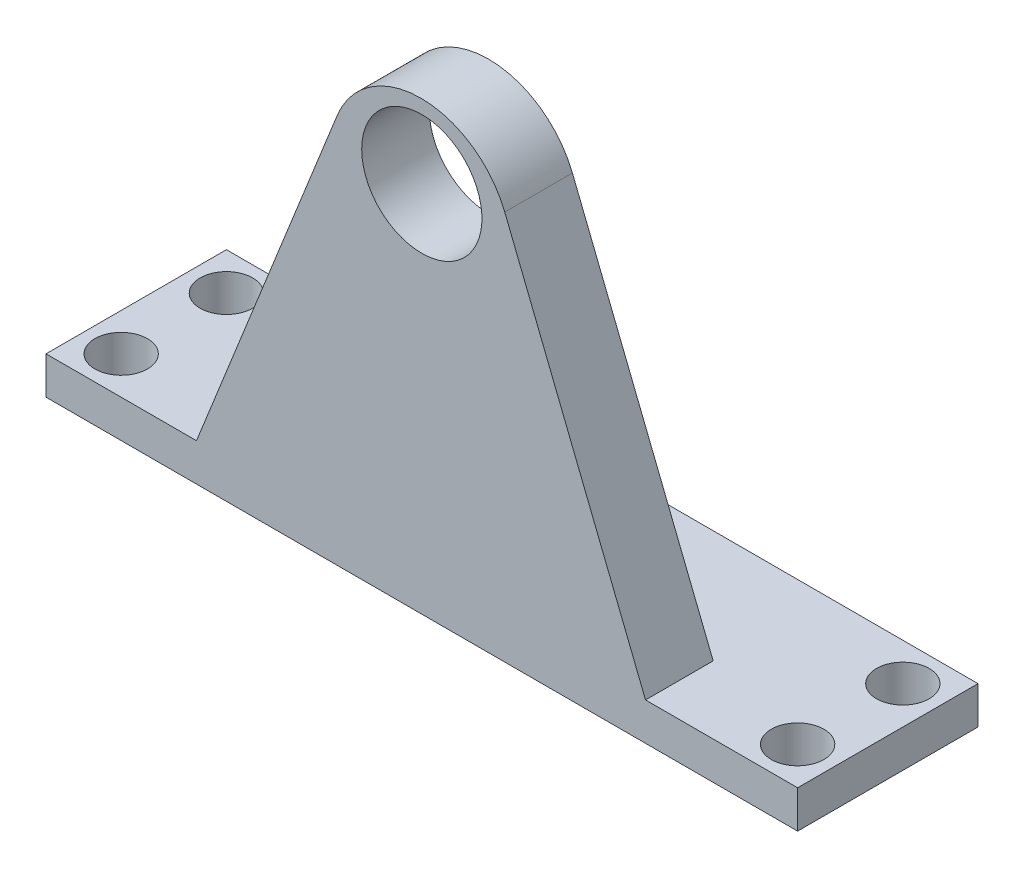
SolidWorks part; units mm, degrees
ref_plane "Front Plane" through (0, 0, 0) normal (0, 0, 1) x (1, 0, 0)
ref_plane "Top Plane" through (0, 0, 0) normal (0, 1, 0) x (1, 0, 0)
ref_plane "Right Plane" through (0, 0, 0) normal (1, 0, 0) x (0, 0, -1)
sketch "Sketch1" plane through (0, 0, 0) normal (0, 1, 0) x (1, 0, 0)
  line L0 (0, 12) -> (0, -12) construction
  line L1 (-50, 12) -> (50, 12)
  line L2 (-50, 12) -> (-50, -12)
  line L3 (-50, -12) -> (50, -12)
  line L4 (50, 12) -> (50, -12)
  line L5 (-45, 0) -> (45, 0) construction
  line L6 (-50, 12) -> (50, -12) construction
  line L7 (-45, 7) -> (-45, -7) construction
  circle A0 centre (-45, 7) radius 3.5
  circle A1 centre (-45, -7) radius 3.5
  circle A2 centre (45, 7) radius 3.5
  circle A3 centre (45, -7) radius 3.5
  dimension "D4" = 90
  dimension "D1" = 100
  dimension "D2" = 24
  dimension "D3" = 45
extrude "Boss-Extrude1" add sketch "Sketch1" along normal blind 5
ref_plane "Plane1" through (0, 0, 3) normal (0, 0, 1) x (1, 0, 0)
sketch "Sketch2" plane through (0, 0, 3) normal (0, 0, 1) x (1, 0, 0)
  line L0 (-50, 5) -> (50, 5) construction
  line L1 (-49.978, 63.276) -> (49.7635, 63.276) construction
  line L2 (-49.978, 63.276) -> (-49.978, 5) construction
  line L3 (-49.978, 5) -> (49.7635, 5) construction
  line L4 (49.7635, 63.276) -> (49.7635, 5) construction
  line L5 (-29.978, 5) -> (29.7635, 5)
  line L6 (-0.1073, 5) -> (-0.1073, 90.7454) construction
  line L7 (-29.978, 5) -> (-11.2501, 51.8549)
  line L8 (11.0356, 51.8549) -> (29.7635, 5)
  arc A0 (11.0356, 51.8549) -> (-11.2501, 51.8549) centre (-0.1073, 47.4011) ccw
  point P13 (-0.1073, 79.733)
  dimension "D3" = 12
  dimension "D1" = 20
  dimension "D2" = 20
extrude "Boss-Extrude2" add sketch "Sketch2" along normal blind 9
sketch "Sketch3" plane through (0, 0, 3) normal (0, 0, -1) x (-1, 0, 0)
  circle A0 centre (0, 49.5783) radius 8
extrude "Cut-Extrude1" cut sketch "Sketch3" against normal through all
